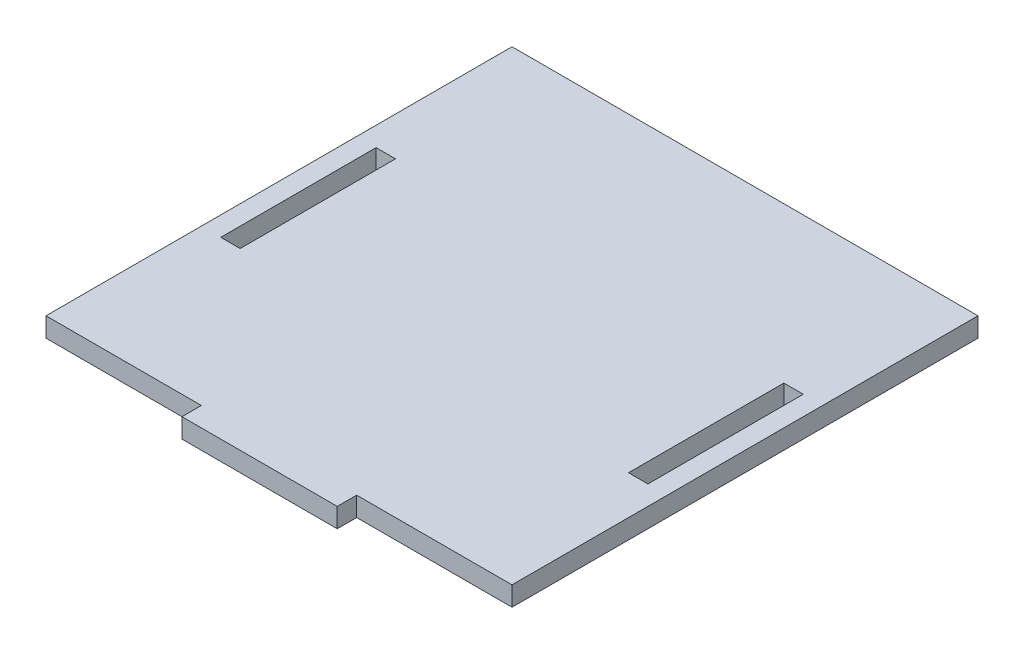
SolidWorks part; units mm, degrees
ref_plane "Front Plane" through (0, 0, 0) normal (0, 0, 1) x (1, 0, 0)
ref_plane "Top Plane" through (0, 0, 0) normal (0, 1, 0) x (1, 0, 0)
ref_plane "Right Plane" through (0, 0, 0) normal (1, 0, 0) x (0, 0, -1)
sketch "Sketch1" plane through (0, 0, 0) normal (0, 1, 0) x (1, 0, 0)
  line L0 (0, 79.375) -> (0, -79.375) construction
  line L1 (76.2, -79.375) -> (-76.2, -79.375)
  line L2 (76.2, -79.375) -> (76.2, 79.375)
  line L3 (76.2, 79.375) -> (-76.2, 79.375)
  line L4 (-76.2, -79.375) -> (-76.2, 79.375)
  line L5 (76.2, -79.375) -> (-76.2, 79.375) construction
  line L6 (76.2, 79.375) -> (-76.2, -79.375) construction
  line L7 (-76.2, -79.375) -> (-25.4, -79.375)
  line L8 (-76.2, -79.375) -> (-76.2, -73.025)
  line L9 (-76.2, -73.025) -> (-25.4, -73.025)
  line L10 (-25.4, -79.375) -> (-25.4, -73.025)
  line L11 (76.2, -73.025) -> (25.4, -73.025)
  line L12 (25.4, -79.375) -> (25.4, -73.025)
  line L13 (76.2, -79.375) -> (25.4, -79.375)
  line L14 (76.2, -79.375) -> (76.2, -73.025)
  line L15 (69.85, -22.225) -> (63.5, -22.225)
  line L16 (-69.85, 28.575) -> (-63.5, 28.575)
  line L17 (-69.85, 28.575) -> (-69.85, -22.225)
  line L18 (-69.85, -22.225) -> (-63.5, -22.225)
  line L19 (-63.5, 28.575) -> (-63.5, -22.225)
  line L20 (63.5, 28.575) -> (63.5, -22.225)
  line L21 (69.85, 28.575) -> (63.5, 28.575)
  line L22 (69.85, 28.575) -> (69.85, -22.225)
  point P0 (0, 0)
  dimension "D1" = 152.4
  dimension "D2" = 158.75
  dimension "D3" = 50.8
  dimension "D4" = 6.35
  dimension "D5" = 6.35
  dimension "D6" = 50.8
  dimension "D7" = 6.35
  dimension "D8" = 50.8
extrude "Boss-Extrude1" add sketch "Sketch1" along normal blind 6.35 contours L1 L12 L11 L2 L3 L4 L9 L10 L16 L19 L18 L17 L21 L22 L15 L20
